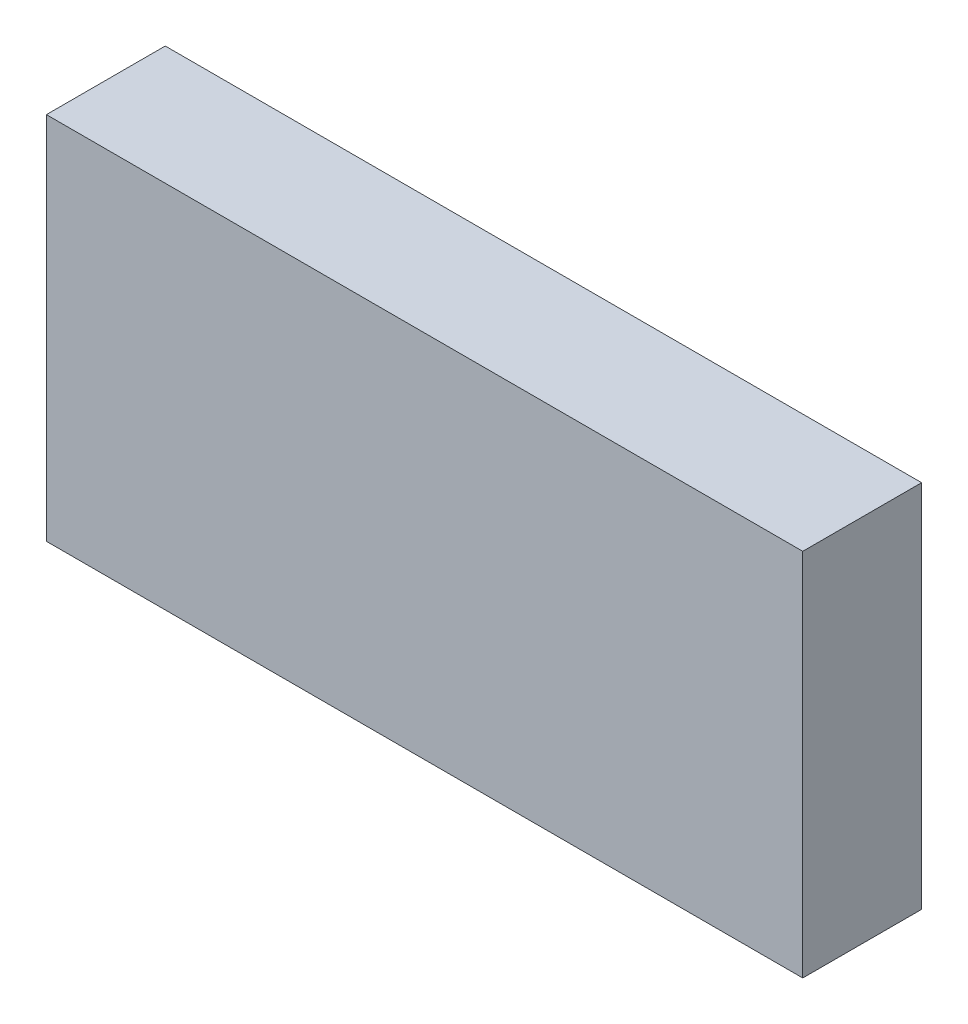
SolidWorks part; units mm, degrees
ref_plane "Front Plane" through (0, 0, 0) normal (0, 0, 1) x (1, 0, 0)
ref_plane "Top Plane" through (0, 0, 0) normal (0, 1, 0) x (1, 0, 0)
ref_plane "Right Plane" through (0, 0, 0) normal (1, 0, 0) x (0, 0, -1)
sketch "Sketch1" plane through (0, 0, 0) normal (0, 0, 1) x (1, 0, 0)
  line L0 (-17.5, 8.55) -> (17.5, -8.55) construction
  line L1 (-17.5, 8.55) -> (17.5, 8.55)
  line L2 (-17.5, 8.55) -> (-17.5, -8.55)
  line L3 (-17.5, -8.55) -> (17.5, -8.55)
  line L4 (17.5, 8.55) -> (17.5, -8.55)
  dimension "D1" = 35
  dimension "D2" = 17.1
extrude "Boss-Extrude1" add sketch "Sketch1" along normal blind 5.5
